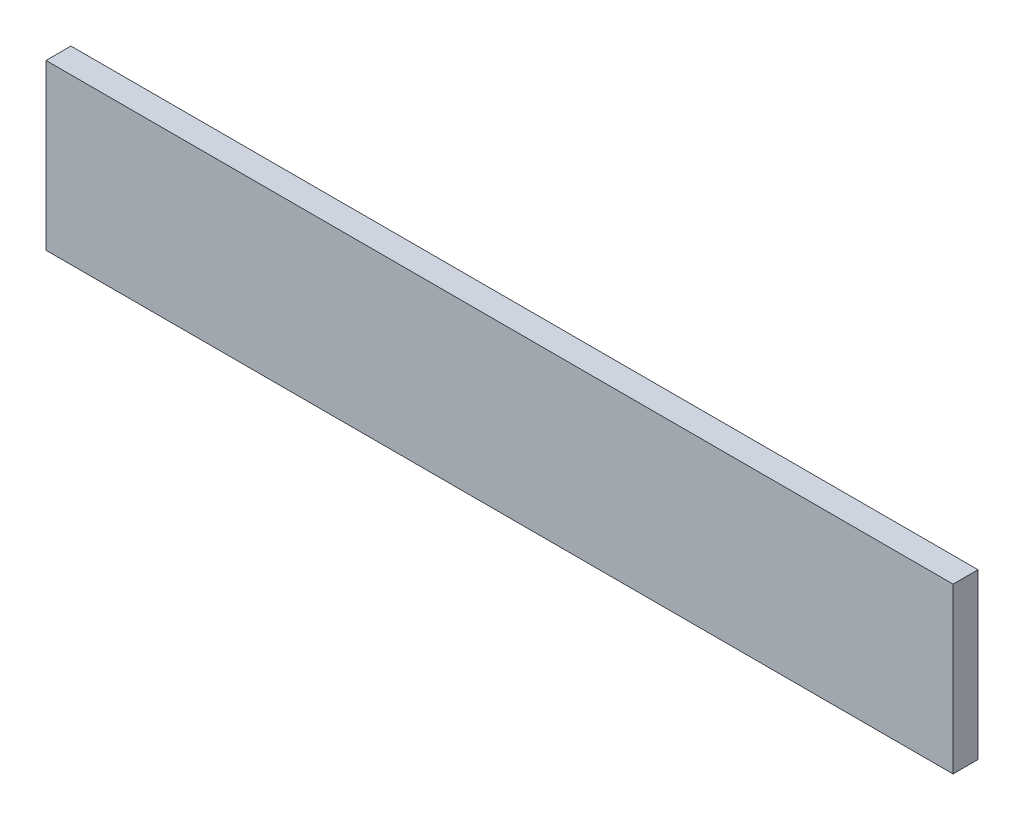
SolidWorks part; units mm, degrees
material "Pine"
ref_plane "Front Plane" through (0, 0, 0) normal (0, 0, 1) x (1, 0, 0)
ref_plane "Top Plane" through (0, 0, 0) normal (0, 1, 0) x (1, 0, 0)
ref_plane "Right Plane" through (0, 0, 0) normal (1, 0, 0) x (0, 0, -1)
sketch "Sketch1" plane through (0, 0, 0) normal (0, 0, 1) x (1, 0, 0)
  line L1 (400, 72.5) -> (-400, 72.5)
  line L2 (400, 72.5) -> (400, -72.5)
  line L3 (400, -72.5) -> (-400, -72.5)
  line L4 (-400, 72.5) -> (-400, -72.5)
  point P4 (-400, 0)
  point P5 (0, -72.5)
  dimension "D1" = 145
  dimension "D2" = 800
extrude "Boss-Extrude1" add sketch "Sketch1" along normal blind 22
